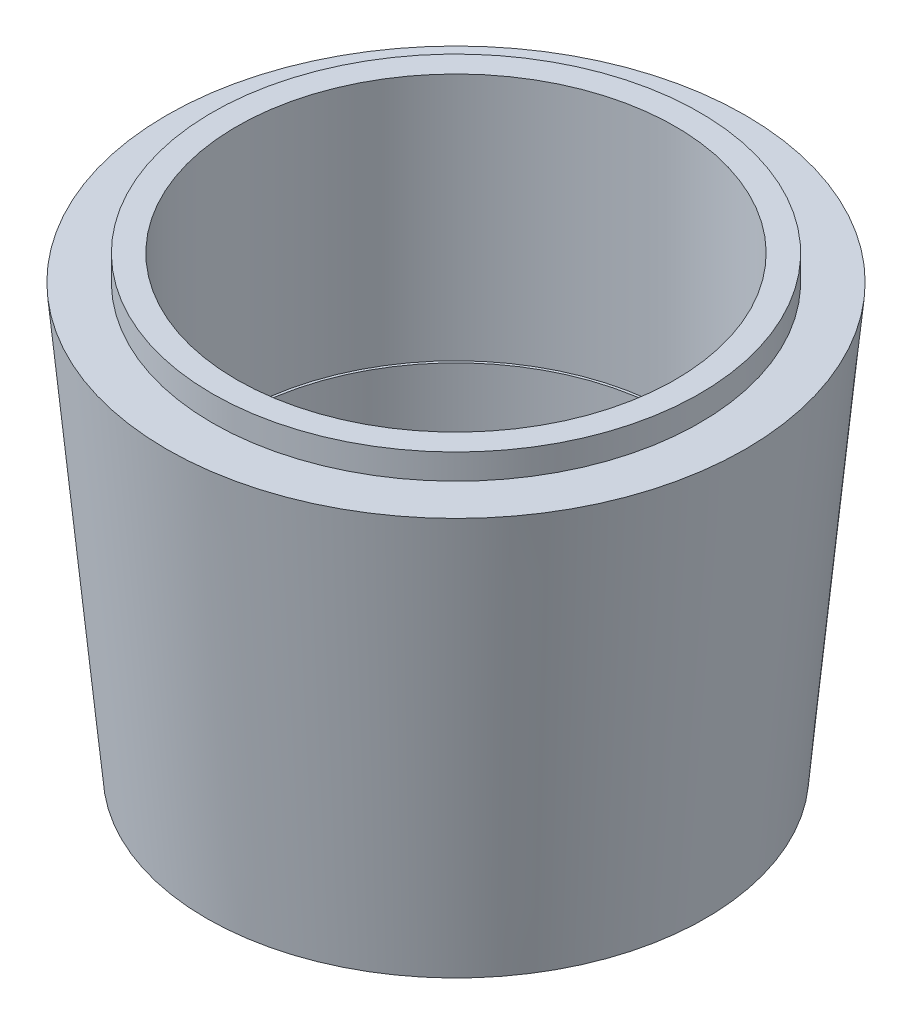
SolidWorks part; units mm, degrees
ref_plane "Front Plane" through (0, 0, 0) normal (0, 0, 1) x (1, 0, 0)
ref_plane "Top Plane" through (0, 0, 0) normal (0, 1, 0) x (1, 0, 0)
ref_plane "Right Plane" through (0, 0, 0) normal (1, 0, 0) x (0, 0, -1)
ref_axis "Axis1" through (0, 5.6415, 0) along (0, -1, 0)
sketch "Sketch1" plane through (0, 0, 0) normal (0, 0, 1) x (1, 0, 0)
  line L0 (20.066, -32.512) -> (22.5446, -42.836)
  line L3 (20.066, -32.512) -> (8.89, 14.0394) construction
  line L7 (22.0472, -22.352) -> (22.0472, 7.62)
  line L8 (22.0472, -22.4282) -> (22.0472, 2.54)
  line L10 (21.7932, -32.512) -> (21.7932, -22.352)
  line L11 (21.7932, -32.512) -> (21.7932, -22.4282)
  line L13 (-21.971, -22.4282) -> (21.971, -22.4282)
  line L14 (21.7932, -22.4282) -> (22.0472, -22.4282)
  line L15 (22.0472, 2.54) -> (24.4983, 2.54)
  line L16 (24.4983, 2.54) -> (24.4983, 0)
  line L17 (24.4983, 0) -> (29.083, 0)
  line L18 (24.5745, 0) -> (24.5745, 6.223) construction
  line L19 (-27.1145, 0) -> (27.1145, 0) construction
  line L20 (20.066, -32.512) -> (21.7932, -32.512)
  line L21 (29.083, 0) -> (25.0846, -42.836)
  line L22 (25.0846, -42.836) -> (22.5446, -42.836)
  dimension "D1" = 2.54
  dimension "D2" = 0.0762
  dimension "D5" = 0.0762
  dimension "D6" = 2.54
  dimension "D3" = 0.0762
  dimension "D4" = 0.0762
revolve "Revolve1" add sketch "Sketch1" angle 360 about axis through (0, 5.6415, 0) along (0, -1, 0)
